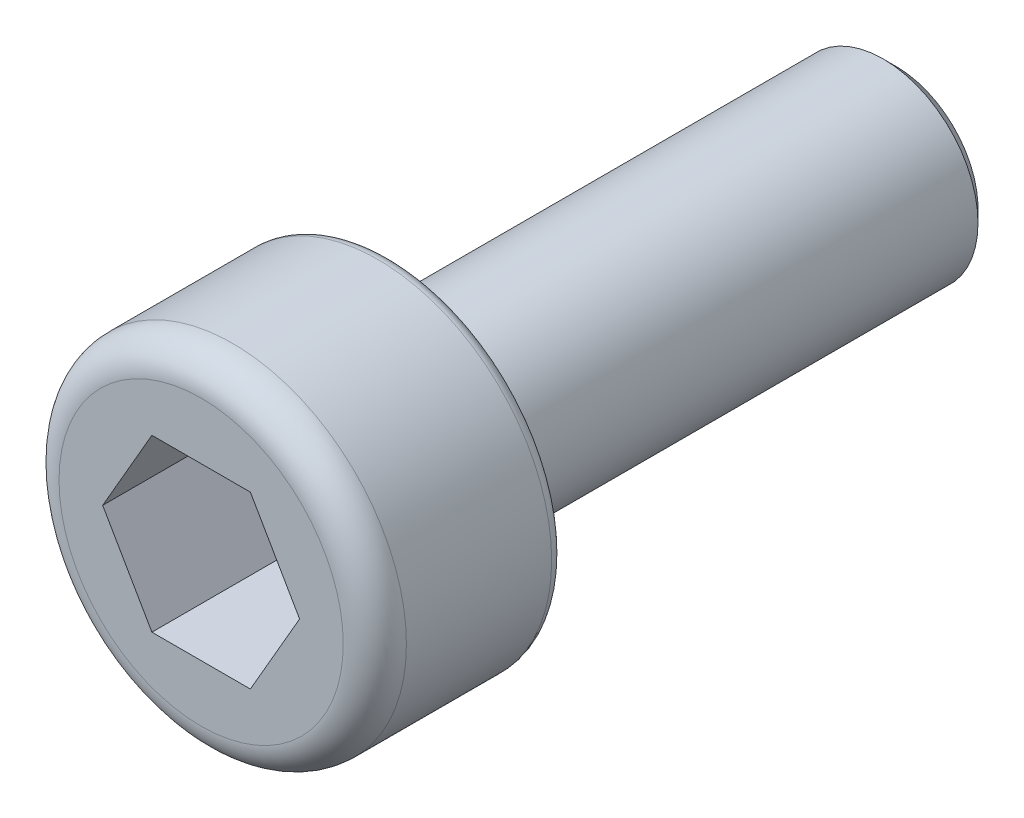
SolidWorks part; units mm, degrees
ref_plane "前视" through (0, 0, 0) normal (0, 0, 1) x (1, 0, 0)
ref_plane "上视" through (0, 0, 0) normal (0, 1, 0) x (1, 0, 0)
ref_plane "右视" through (0, 0, 0) normal (1, 0, 0) x (0, 0, -1)
sketch "草图1" plane through (0, 0, 0) normal (0, 0, 1) x (1, 0, 0)
  circle A0 centre (0, 0) radius 2.75
  dimension "D1" = 5.5
extrude "凸台-拉伸1" add sketch "草图1" along normal blind 3
fillet "圆角1" radius 0.5 1 edges at (2.75, 0, 3)
sketch "草图2" plane through (0, 0, 3) normal (0, 0, 1) x (1, 0, 0)
  line L1 (1.5588, 0) -> (0.7794, 1.35)
  line L2 (0.7794, 1.35) -> (-0.7794, 1.35)
  line L3 (-0.7794, 1.35) -> (-1.5588, 0)
  line L4 (-1.5588, 0) -> (-0.7794, -1.35)
  line L5 (-0.7794, -1.35) -> (0.7794, -1.35)
  line L6 (0.7794, -1.35) -> (1.5588, 0)
  circle A0 centre (0, 0) radius 1.35 construction
  dimension "D1" = 2.7
extrude "切除-拉伸1" cut sketch "草图2" against normal blind 2
sketch "草图3" plane through (0, 0, 0) normal (0, 0, -1) x (-1, 0, 0)
  circle A0 centre (0, 0) radius 1.5
  dimension "D1" = 3
extrude "凸台-拉伸2" add sketch "草图3" along normal blind 8
chamfer "倒角1" distance 0.2 angle 45 1 edges at (-1.5, 0, -8)
fillet "圆角2" radius 0.2 1 edges at (2.75, 0, 0)
